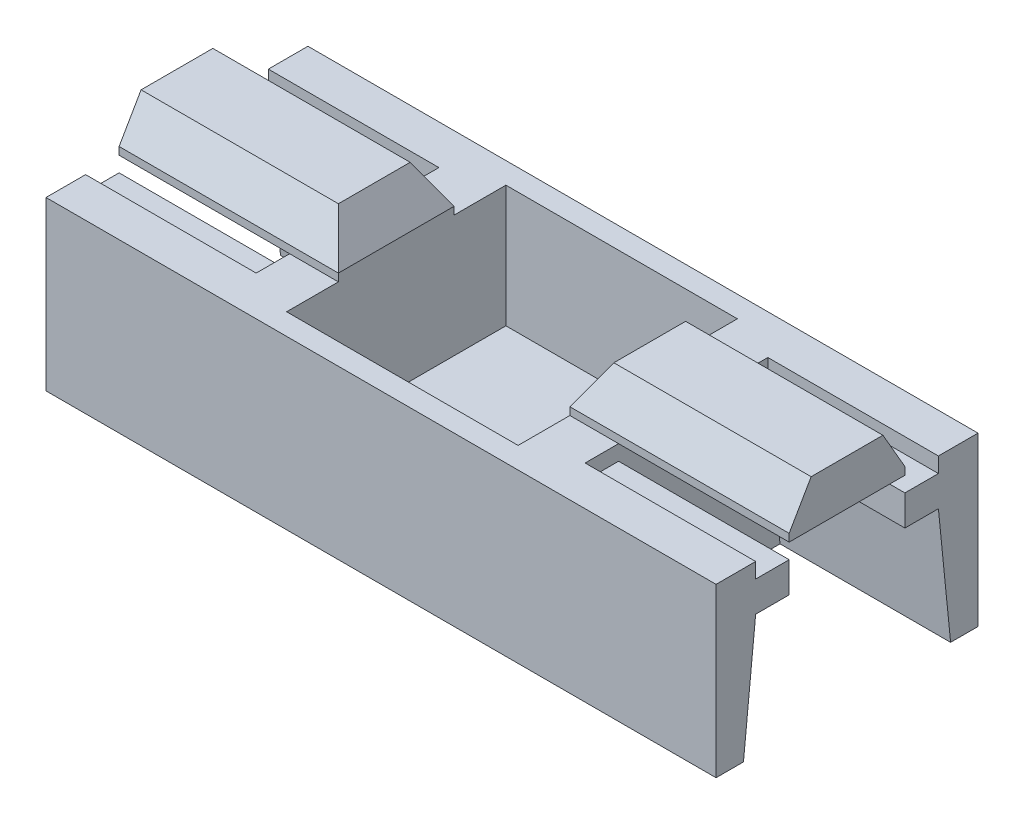
SolidWorks part; units mm, degrees
ref_plane "Plan de face" through (0, 0, 0) normal (0, 0, 1) x (1, 0, 0)
ref_plane "Plan de dessus" through (0, 0, 0) normal (0, 1, 0) x (1, 0, 0)
ref_plane "Plan de droite" through (0, 0, 0) normal (1, 0, 0) x (0, 0, -1)
sketch "Esquisse1" plane through (0, 0, 0) normal (0, 0, 1) x (1, 0, 0)
  line L1 (0, 0) -> (22, 0)
  line L2 (0, 0) -> (0, 7)
  line L3 (0, 7) -> (22, 7)
  line L4 (22, 0) -> (22, 7)
extrude "Boss.-Extru.1" add sketch "Esquisse1" along normal blind 8.6
sketch "Esquisse2" plane through (0, 7, 0) normal (0, 1, 0) x (1, 0, 0)
  line L0 (23.1015, -4.3) -> (5.719, -4.3) construction
  line L1 (11, -9.8466) -> (11, 1.25) construction
  line L2 (7.2, -9.8466) -> (7.2, 1.5707) construction
  line L3 (23.1015, -0.7) -> (5.719, -0.7) construction
  line L4 (-0.6953, 0) -> (22.7166, 0) construction
  line L5 (-0.3318, -8.6) -> (23.1015, -8.6) construction
  line L6 (23.1015, -7.9) -> (5.719, -7.9) construction
  line L7 (14.8, -9.8466) -> (14.8, 1.25) construction
  line L9 (7.2, -0.7) -> (14.8, -0.7)
  line L10 (7.2, -0.7) -> (7.2, -7.9)
  line L11 (7.2, -7.9) -> (14.8, -7.9)
  line L12 (14.8, -0.7) -> (14.8, -7.9)
  dimension "D1" = 3.8
  dimension "D2" = 0.7
  dimension "D3" = 0.7
  dimension "D4" = 3.8
extrude "Enlèv. mat.-Extru.1" cut sketch "Esquisse2" against normal blind 5.5
sketch "Esquisse3" plane through (22, 0, 0) normal (1, 0, 0) x (0, 0, -1)
  line L0 (-4.3, -0.8594) -> (-4.3, 7.6476) construction
  line L1 (-8.6, -0.2242) -> (-8.6, 8.0711) construction
  line L2 (-6.2, -0.2242) -> (-6.2, 7.6476) construction
  line L3 (-10.1789, 5.5) -> (-5.969, 5.5) construction
  line L4 (-9.9921, 0) -> (0.9935, 0) construction
  line L5 (0.2213, 7) -> (-9.2199, 7) construction
  line L6 (0, 7) -> (-2.4, 7)
  line L7 (-8.6, 5.5) -> (-6.2, 5.5)
  line L8 (-8.6, 5.5) -> (-8.6, 7)
  line L9 (-8.6, 7) -> (-6.2, 7)
  line L10 (-6.2, 5.5) -> (-6.2, 7)
  line L11 (-2.4, 5.5) -> (-2.4, 7)
  line L12 (0, 5.5) -> (-2.4, 5.5)
  line L13 (0, 5.5) -> (0, 7)
  dimension "D1" = 5.5
  dimension "D2" = 2.4
extrude "Enlèv. mat.-Extru.2" cut sketch "Esquisse3" against normal through all
ref_plane "Plan1" through (11, 0, 0) normal (1, 0, 0) x (0, 0, -1)
sketch "Esquisse6" plane through (22, 0, 0) normal (1, 0, 0) x (0, 0, -1)
  line L0 (-4.3, 7.7583) -> (-4.3, -0.2277) construction
  line L1 (-8.9419, 5.5) -> (0.827, 5.5) construction
  line L2 (-9.3533, 0) -> (0.6582, 0) construction
  line L3 (-8.6, -0.597) -> (-8.6, 6.3235) construction
  line L4 (-9.5115, 4) -> (-3.7515, 4) construction
  line L5 (-9.5115, 5) -> (-3.8781, 5) construction
  line L6 (-7.7, -0.597) -> (-7.7, 0.7428) construction
  line L7 (-7.3, 6.3235) -> (-7.3, 3.2958) construction
  line L8 (-6.2, 7.7583) -> (-6.2, 3.2958) construction
  line L9 (-1.3, 5.5) -> (-7.3, 5.5)
  line L10 (-7.3, 5.5) -> (-7.3, 5)
  line L11 (-7.3, 5) -> (-6.2, 5)
  line L12 (-6.2, 5) -> (-6.2, 4)
  line L13 (-6.2, 4) -> (-7.3, 4)
  line L14 (-7.3, 4) -> (-7.7, 0)
  line L15 (-7.7, 0) -> (-0.9, 0)
  line L16 (-1.3, 4) -> (-0.9, 0)
  line L17 (-2.4, 4) -> (-1.3, 4)
  line L18 (-2.4, 5) -> (-2.4, 4)
  line L19 (-1.3, 5) -> (-2.4, 5)
  line L20 (-1.3, 5.5) -> (-1.3, 5)
  dimension "D1" = 4
  dimension "D2" = 0.9
  dimension "D3" = 1.3
  dimension "D4" = 1
  dimension "D5" = 1.9
extrude "Enlèv. mat.-Extru.5" cut sketch "Esquisse6" against normal blind 5.6
chamfer "Chanfrein1" distance 1.25 angle 30 3 edges at (18.4, 7, 2.4) (14.8, 7, 4.3) (18.4, 7, 6.2)
mirror "Symétrie4" about plane through (11, 0, 0) normal (1, 0, 0) of "Enlèv. mat.-Extru.5"
chamfer "Chanfrein2" distance 1.25 angle 30 3 edges at (3.6, 7, 2.4) (7.2, 7, 4.3) (3.6, 7, 6.2)
